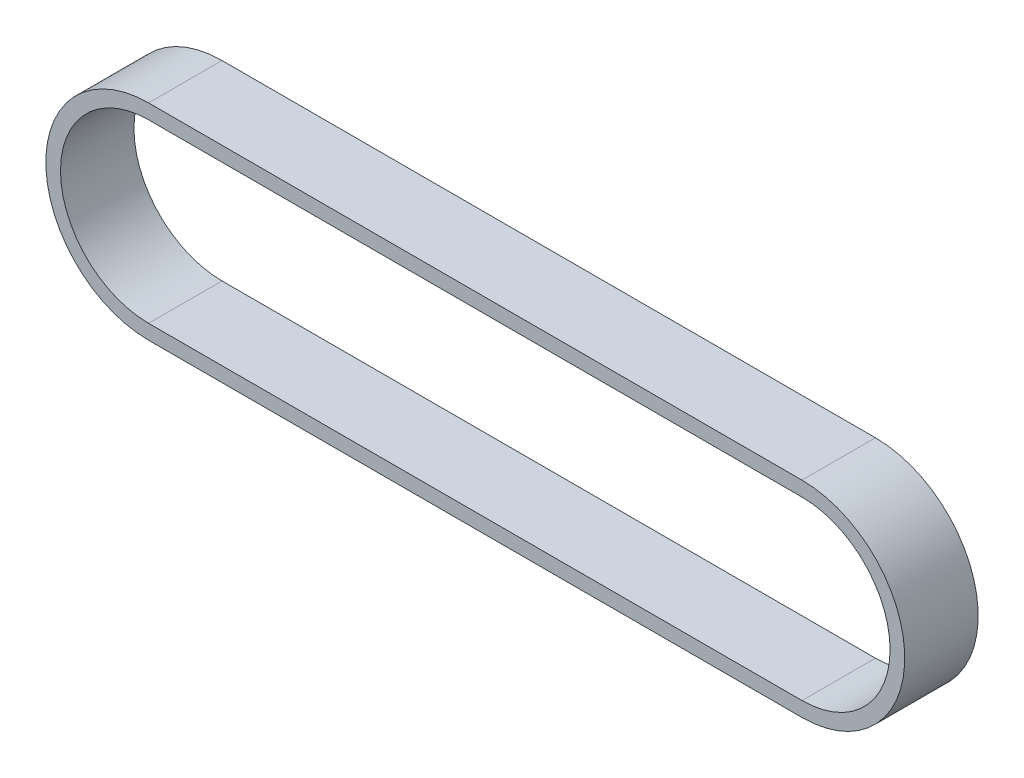
SolidWorks part; units mm, degrees
ref_plane "前视基准面" through (0, 0, 0) normal (0, 0, 1) x (1, 0, 0)
ref_plane "上视基准面" through (0, 0, 0) normal (0, 1, 0) x (1, 0, 0)
ref_plane "右视基准面" through (0, 0, 0) normal (1, 0, 0) x (0, 0, -1)
other "Configuration Table"
sketch "草图1" plane through (0, 0, 0) normal (0, 0, 1) x (1, 0, 0)
  line L0 (0, 0) -> (89, 0) construction
  line L1 (0, 14) -> (89, 14)
  line L2 (0, -14) -> (89, -14)
  line L3 (0, 12) -> (89, 12)
  line L4 (0, -12) -> (89, -12)
  arc A0 (0, 14) -> (0, -14) centre (0, 0) ccw
  arc A1 (89, -14) -> (89, 14) centre (89, 0) ccw
  arc A2 (89, -12) -> (89, 12) centre (89, 0) ccw
  arc A3 (0, 12) -> (0, -12) centre (0, 0) ccw
  point P3 (44.5, 0)
  dimension "D2" = 14
  dimension "D1" = 89
  dimension "D3" = 2
extrude "凸台-拉伸1" add sketch "草图1" along normal blind 10
